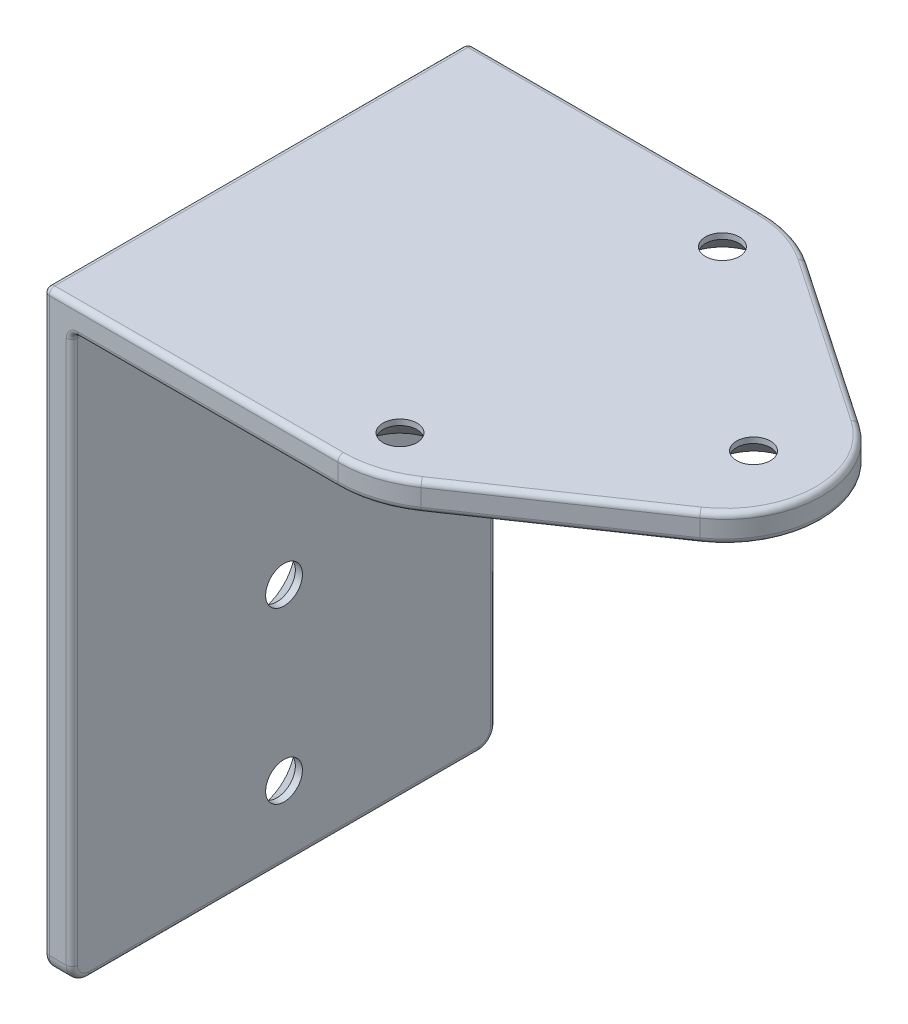
SolidWorks part; units mm, degrees
ref_plane "Plan de face" through (0, 0, 0) normal (0, 0, 1) x (1, 0, 0)
ref_plane "Plan de dessus" through (0, 0, 0) normal (0, 1, 0) x (1, 0, 0)
ref_plane "Plan de droite" through (0, 0, 0) normal (1, 0, 0) x (0, 0, -1)
sketch "Esquisse1" plane through (0, 0, 0) normal (0, 0, 1) x (1, 0, 0)
  line L0 (0, 43.2609) -> (0, -44.7101) construction
  line L1 (54.061, 0) -> (-50.4318, 0) construction
  line L2 (50, 0) -> (50, 5)
  line L3 (50, 5) -> (-50, 5)
  line L4 (-50, 5) -> (-50, -100)
  line L5 (-50, -100) -> (-45, -100)
  line L6 (-45, -100) -> (-45, 0)
  line L7 (-45, 0) -> (50, 0)
  dimension "D1" = 5
  dimension "D2" = 105
  dimension "D3" = 100
extrude "Boss.-Extru.1" add sketch "Esquisse1" along normal mid plane 75
fillet "Congé1" radius 1 1 edges at (-50, 5, 0)
fillet "Congé2" radius 1 1 edges at (-45, 0, 0)
sketch "Esquisse2" plane through (0, 5, 0) normal (0, 1, 0) x (1, 0, 0)
  line L0 (-65.3935, 0) -> (93.2305, 0) construction
  line L1 (0, 40.6081) -> (0, -39.6066) construction
  line L2 (50, 37.5) -> (-49, 37.5) construction
  line L3 (50, -37.5) -> (-49, -37.5) construction
  line L4 (13.2647, 34.026) -> (42.575, 14.0471)
  line L5 (42.575, -14.0471) -> (13.2647, -34.026)
  line L6 (2, 37.5) -> (2, -37.5) construction
  line L7 (2, 37.5) -> (2, 49.3574)
  line L8 (2, 49.3574) -> (93.2305, 49.3574)
  line L9 (93.2305, 49.3574) -> (93.2305, -49.3574)
  line L10 (93.2305, -49.3574) -> (2, -49.3574)
  line L11 (2, -49.3574) -> (2, -37.5)
  line L13 (50, -37.5) -> (50, 37.5) construction
  arc A0 (42.575, -14.0471) -> (42.575, 14.0471) centre (33, 0) ccw
  arc A1 (2, -37.5) -> (13.2647, -34.026) centre (2, -17.5) ccw
  arc A2 (13.2647, 34.026) -> (2, 37.5) centre (2, 17.5) ccw
  dimension "D1" = 48
  dimension "D2" = 20
  dimension "D3" = 17
extrude "Enlèv. mat.-Extru.1" cut sketch "Esquisse2" against normal through all
fillet "Congé3" radius 3 1 edges at (-47.5, -100, -37.5)
fillet "Congé4" radius 3 1 edges at (-47.5, -100, 37.5)
sketch "Esquisse5" plane through (0, 0, 0) normal (0, 0, 1) x (1, 0, 0)
  line L0 (-72.135, -87) -> (-12.3252, -87) construction
  line L1 (-45, -100) -> (-50, -100) construction
  line L2 (-44, -87) -> (-44, -83.75)
  line L3 (-44, -83.75) -> (-46.25, -83.75)
  line L4 (-46.25, -83.75) -> (-50, -80)
  line L5 (-50, -80) -> (-50, -87)
  line L6 (-50, -87) -> (-44, -87)
  line L7 (-50, 4) -> (-50, -97) construction
  line L8 (-45, -97) -> (-45, -1) construction
  dimension "D1" = 13
  dimension "D2" = 45
  dimension "D3" = 7
  dimension "D4" = 3.75
  dimension "D5" = 3.25
  dimension "D6" = 1
revolve "Enlèvement de matière-Révolution2" cut sketch "Esquisse5" angle 360 about L0
pattern_linear "Répétition linéaire2" count 3 spacing 30 along (0, 1, 0) of "Enlèvement de matière-Révolution2"
fillet "Congé5" radius 1 28 edges at (7.8941, 0, -36.6118) (-21, 0, -37.5) (-44.7071, -0.2929, -37.5) (-45, -49, -37.5) (-45, -99.1213, -36.6213) (-45, -100, 0) (-45, -99.1213, 36.6213) (-45, -49, 37.5) (-44.7071, -0.2929, 37.5) (-21, 0, 37.5) (7.8941, 0, 36.6118) (27.9198, 0, 24.0365) (50, 0, 0) (27.9198, 5, -24.0365) (7.8941, 5, -36.6118) (-23.5, 5, -37.5) (-49.7071, 4.7071, -37.5) (-50, -46.5, -37.5) (-50, -99.1213, -36.6213) (-50, -100, 0) (-50, -99.1213, 36.6213) (-50, -46.5, 37.5) (-49.7071, 4.7071, 37.5) (-23.5, 5, 37.5) (7.8941, 5, 36.6118) (27.9198, 5, 24.0365) (27.9198, 0, -24.0365) (50, 5, 0)
sketch "Esquisse6" plane through (0, 0, 0) normal (0, 0, 1) x (1, 0, 0)
  line L0 (38, 8.2576) -> (38, -6.7274) construction
  line L1 (50, 1) -> (50, 4) construction
  line L2 (38, 6) -> (35, 6)
  line L3 (35, 6) -> (35, 4)
  line L4 (35, 4) -> (30, -1)
  line L5 (30, -1) -> (38, -1)
  line L6 (38, -1) -> (38, 6)
  line L7 (42.0117, 0) -> (49, 0) construction
  line L8 (49, 5) -> (42.0117, 5) construction
  dimension "D1" = 12
  dimension "D2" = 3
  dimension "D3" = 45
  dimension "D4" = 4
  dimension "D5" = 1
  dimension "D6" = 1
revolve "Enlèvement de matière-Révolution3" cut sketch "Esquisse6" angle 360 about L0
ref_plane "Plan1" through (0, 0, 28.5) normal (0, 0, 1) x (1, 0, 0)
sketch "Esquisse10" plane through (0, 0, 28.5) normal (0, 0, 1) x (1, 0, 0)
  line L0 (4, 7.7322) -> (4, -8.7378) construction
  line L1 (4, 6) -> (1, 6)
  line L2 (1, 6) -> (1, 4)
  line L3 (1, 4) -> (-4, -1)
  line L4 (-4, -1) -> (4, -1)
  line L5 (4, -1) -> (4, 6)
  line L6 (12.7014, 5) -> (42.0117, 5) construction
  line L7 (42.0117, 0) -> (12.7014, 0) construction
  line L8 (50, 1) -> (50, 4) construction
  dimension "D1" = 3
  dimension "D2" = 45
  dimension "D3" = 1
  dimension "D4" = 1
  dimension "D5" = 4
  dimension "D6" = 46
revolve "Enlèvement de matière-Révolution5" cut sketch "Esquisse10" angle 360 about L0
mirror "Symétrie1" about plane through (0, 0, 0) normal (0, 0, 1) of "Enlèvement de matière-Révolution5"
